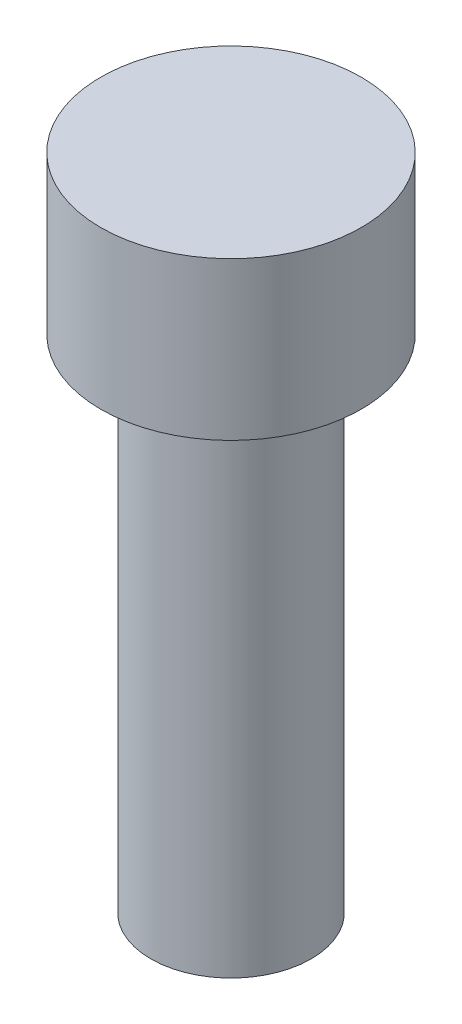
SolidWorks part; units mm, degrees
ref_plane "Plan de face" through (0, 0, 0) normal (0, 0, 1) x (1, 0, 0)
ref_plane "Plan de dessus" through (0, 0, 0) normal (0, 1, 0) x (1, 0, 0)
ref_plane "Plan de droite" through (0, 0, 0) normal (1, 0, 0) x (0, 0, -1)
sketch "Esquisse1" plane through (0, 0, 0) normal (0, 0, 1) x (1, 0, 0)
  line L0 (0, 0) -> (6.5, 0)
  line L1 (6.5, 0) -> (6.5, -7.8521)
  line L2 (6.5, -7.8521) -> (4, -7.8521)
  line L3 (4, -7.8521) -> (4, -32.8521)
  line L4 (4, -32.8521) -> (0, -32.8521)
  line L5 (0, 0) -> (0, -13.9782) construction
  line L6 (0, 0) -> (0, -32.8521)
revolve "Révolution1" add sketch "Esquisse1" angle 360 about L5
